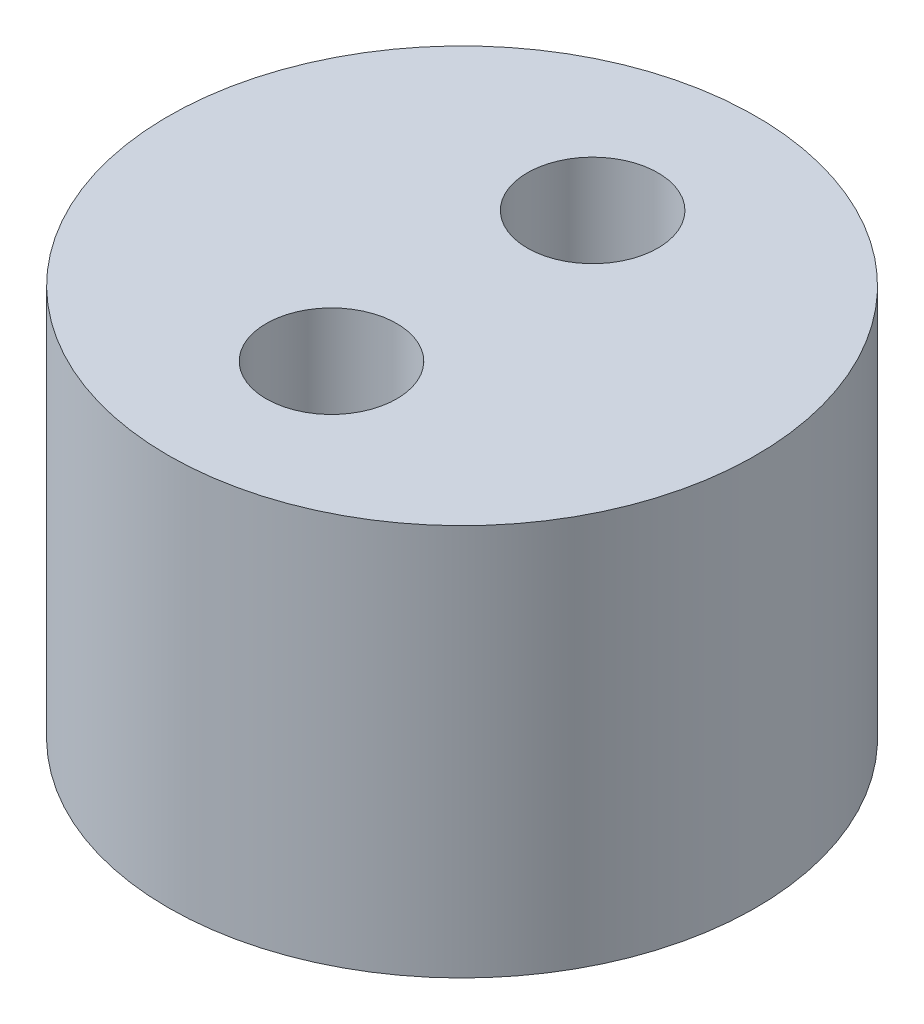
SolidWorks part; units mm, degrees
ref_plane "Front Plane" through (0, 0, 0) normal (0, 0, 1) x (1, 0, 0)
ref_plane "Top Plane" through (0, 0, 0) normal (0, 1, 0) x (1, 0, 0)
ref_plane "Right Plane" through (0, 0, 0) normal (1, 0, 0) x (0, 0, -1)
sketch "Sketch1" plane through (0, 0, 0) normal (0, 1, 0) x (1, 0, 0)
  line L0 (0, 5) -> (0, -5) construction
  circle A0 centre (0, 0) radius 11.25
  circle A1 centre (0, 5) radius 2.5
  circle A2 centre (0, -5) radius 2.5
  point P6 (0, 0)
  dimension "D1" = 22.5
  dimension "D2" = 10
  dimension "D3" = 5
  dimension "D4" = 5
extrude "Boss-Extrude1" add sketch "Sketch1" along normal blind 15
